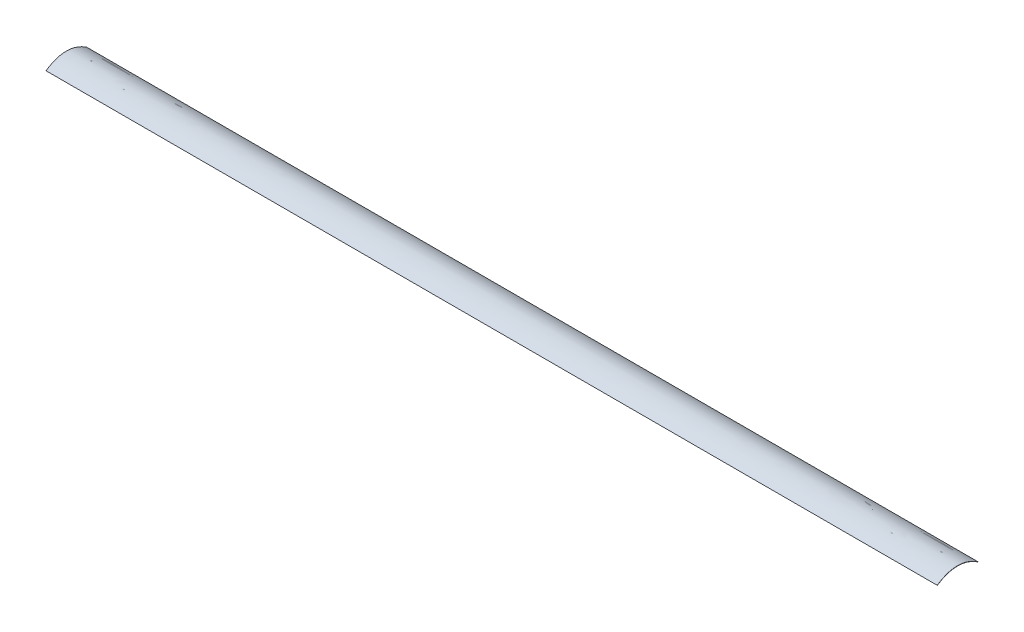
SolidWorks part; units mm, degrees
ref_plane "Front" through (0, 0, 0) normal (0, 0, 1) x (1, 0, 0)
ref_plane "Top" through (0, 0, 0) normal (0, 1, 0) x (1, 0, 0)
ref_plane "Right" through (0, 0, 0) normal (1, 0, 0) x (0, 0, -1)
sketch "Sketch1" plane through (0, 0, 0) normal (1, 0, 0) x (0, 0, -1)
  line L0 (7.55, 0) -> (7.45, 0)
  line L1 (-7.45, 0) -> (-7.55, 0)
  spline S0 degree 2 poles (7.55, 0) (0, 5.1) (-7.55, 0) knots 0 0 0 1 1 1
  spline S1 degree 2 poles (-7.45, 0) (0, 4.9) (7.45, 0) knots 0 0 0 1 1 1
  dimension "D6" = 2.45
  dimension "D1" = 7.55
  dimension "D2" = 7.55
  dimension "D3" = 2.55
  dimension "D4" = 7.45
  dimension "D5" = 7.45
  dimension "D7" = 0
  dimension "D8" = 0
  dimension "D9" = 0
extrude "Boss-Extrude1" add sketch "Sketch1" along normal mid plane 330.2
